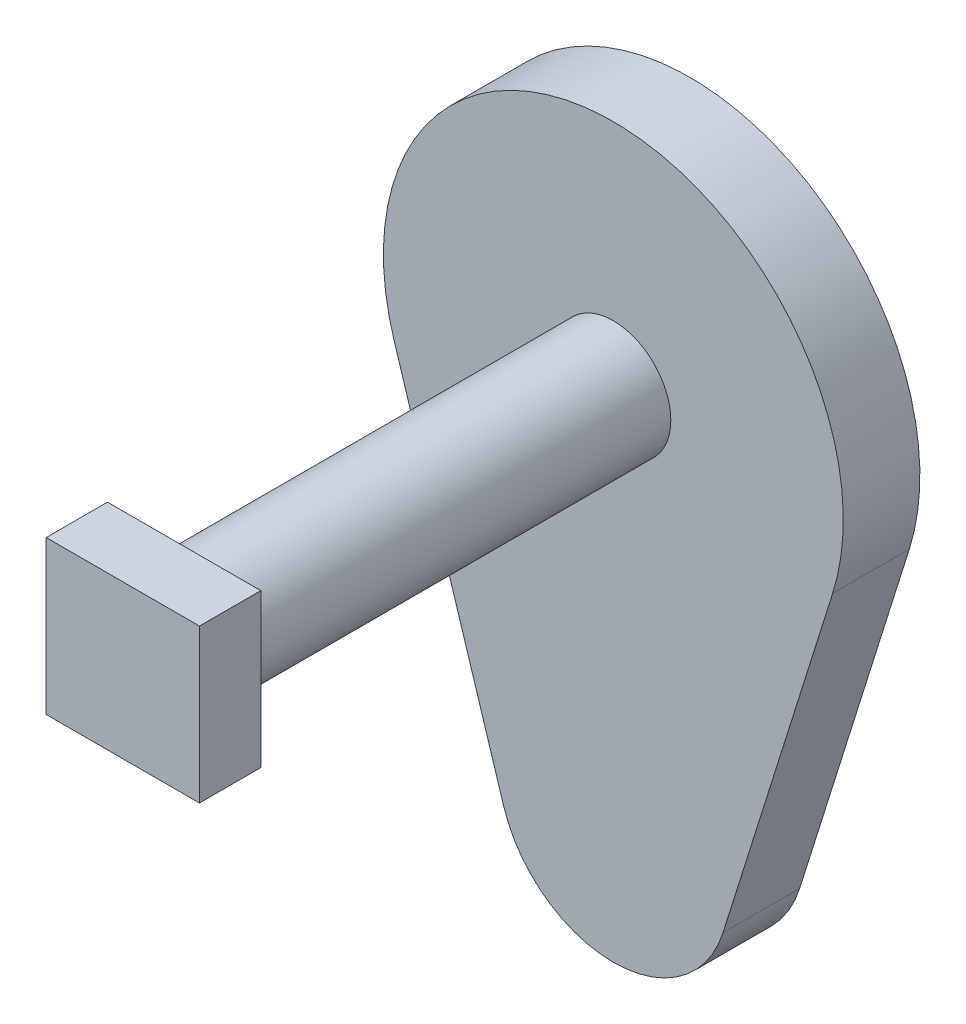
SolidWorks part; units mm, degrees
ref_plane "Front Plane" through (0, 0, 0) normal (0, 0, 1) x (1, 0, 0)
ref_plane "Top Plane" through (0, 0, 0) normal (0, 1, 0) x (1, 0, 0)
ref_plane "Right Plane" through (0, 0, 0) normal (1, 0, 0) x (0, 0, -1)
sketch "Sketch1" plane through (0, 0, 0) normal (0, 0, 1) x (1, 0, 0)
  line L0 (-28.6182, 41) -> (-14.3091, -4.5)
  line L1 (28.6182, 41) -> (14.3091, -4.5)
  arc A0 (28.6182, 41) -> (-28.6182, 41) centre (0, 50) ccw
  arc A1 (-14.3091, -4.5) -> (14.3091, -4.5) centre (0, 0) ccw
  dimension "D1" = 60
  dimension "D2" = 30
  dimension "D3" = 50
extrude "Boss-Extrude1" add sketch "Sketch1" along normal blind 10
sketch "Sketch2" plane through (0, 0, 10) normal (0, 0, 1) x (1, 0, 0)
  circle A0 centre (0, 50) radius 7.5
  arc A1 (28.6182, 41) -> (-28.6182, 41) centre (0, 50) ccw construction
  dimension "D1" = 15
extrude "Boss-Extrude2" add sketch "Sketch2" along normal blind 56
sketch "Sketch3" plane through (0, 0, 66) normal (0, 0, 1) x (1, 0, 0)
  line L5 (-10, 40) -> (10, 40)
  line L6 (-10, 40) -> (-10, 60)
  line L7 (-10, 60) -> (10, 60)
  line L8 (10, 40) -> (10, 60)
  line L9 (-10, 40) -> (10, 60) construction
  line L10 (-10, 60) -> (10, 40) construction
  point P4 (0, 50)
  dimension "D1" = 20
  dimension "D2" = 20
extrude "Boss-Extrude3" add sketch "Sketch3" along normal blind 8
